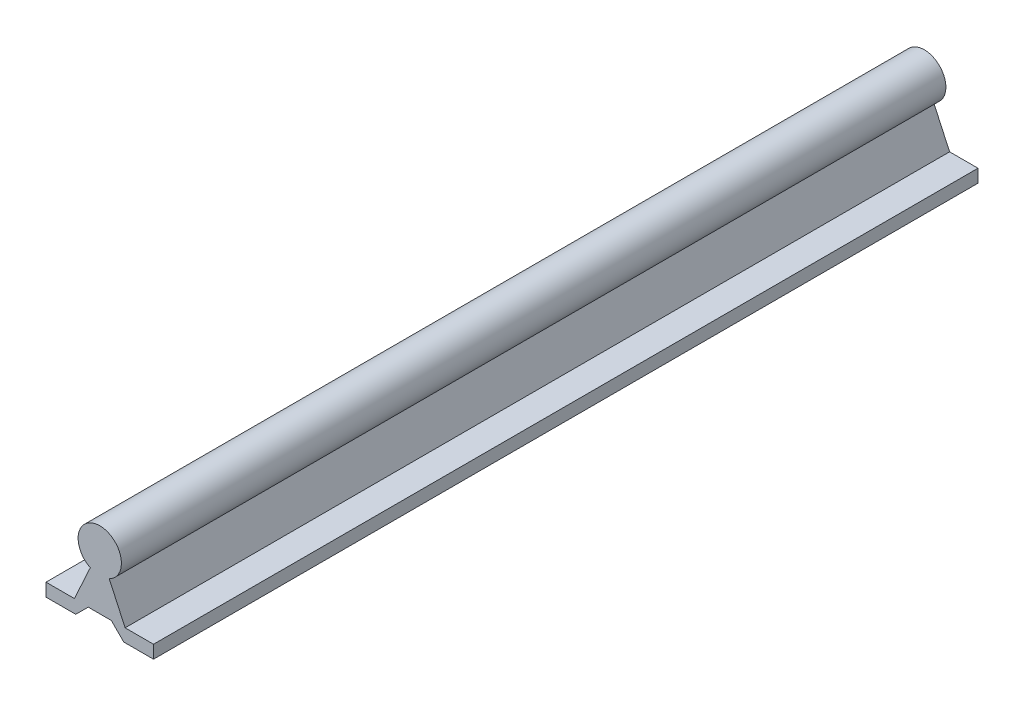
SolidWorks part; units mm, degrees
ref_plane "Front Plane" through (0, 0, 0) normal (0, 0, 1) x (1, 0, 0)
ref_plane "Top Plane" through (0, 0, 0) normal (0, 1, 0) x (1, 0, 0)
ref_plane "Right Plane" through (0, 0, 0) normal (1, 0, 0) x (0, 0, -1)
sketch "Sketch1" plane through (0, 0, 0) normal (0, 0, 1) x (1, 0, 0)
  line L0 (3.5, 17.6063) -> (9.375, 4.8)
  line L1 (19.875, 4.8) -> (9.375, 4.8)
  line L2 (19.875, 4.8) -> (19.875, 0)
  line L3 (19.875, 0) -> (8.875, 0)
  line L4 (-19.875, 4.8) -> (-19.875, 0)
  line L5 (19.875, 4.8) -> (-19.875, 0) construction
  line L6 (19.875, 0) -> (-19.875, 4.8) construction
  line L7 (-3.5, 17.6063) -> (-9.375, 4.8)
  line L8 (9.375, 4.8) -> (-9.375, 4.8) construction
  line L9 (-9.375, 4.8) -> (-19.875, 4.8)
  line L10 (-19.875, 0) -> (-8.875, 0)
  line L11 (-8.875, 0) -> (-4.275, 4.6)
  line L12 (-4.275, 4.6) -> (4.275, 4.6)
  line L13 (19.875, 0) -> (8.875, 0)
  line L14 (8.875, 0) -> (4.275, 4.6)
  line L15 (8.875, 0) -> (-8.875, 0) construction
  line L16 (-8.875, 0) -> (-19.875, 0)
  arc A0 (3.5, 17.6063) -> (-3.5, 17.6063) centre (0, 24.8) ccw
  arc A1 (-3.5, 17.6063) -> (3.5, 17.6063) centre (0, 24.8) ccw construction
  point P0 (0, 2.4)
  dimension "D1" = 16
  dimension "D2" = 24.8
  dimension "D3" = 39.75
  dimension "D4" = 4.8
  dimension "D5" = 7
  dimension "D6" = 18.75
  dimension "D7" = 4.6
  dimension "D8" = 11
  dimension "D9" = 11
  dimension "D10" = 45
extrude "Boss-Extrude1" add sketch "Sketch1" along normal blind 304.8 contours L0 A0 L7 L9 L4 L10 L11 L12 L14 L3 L2 L1
equation "\"length\"= 12in"
equation "\"D1@Boss-Extrude1\"=\"length\""
